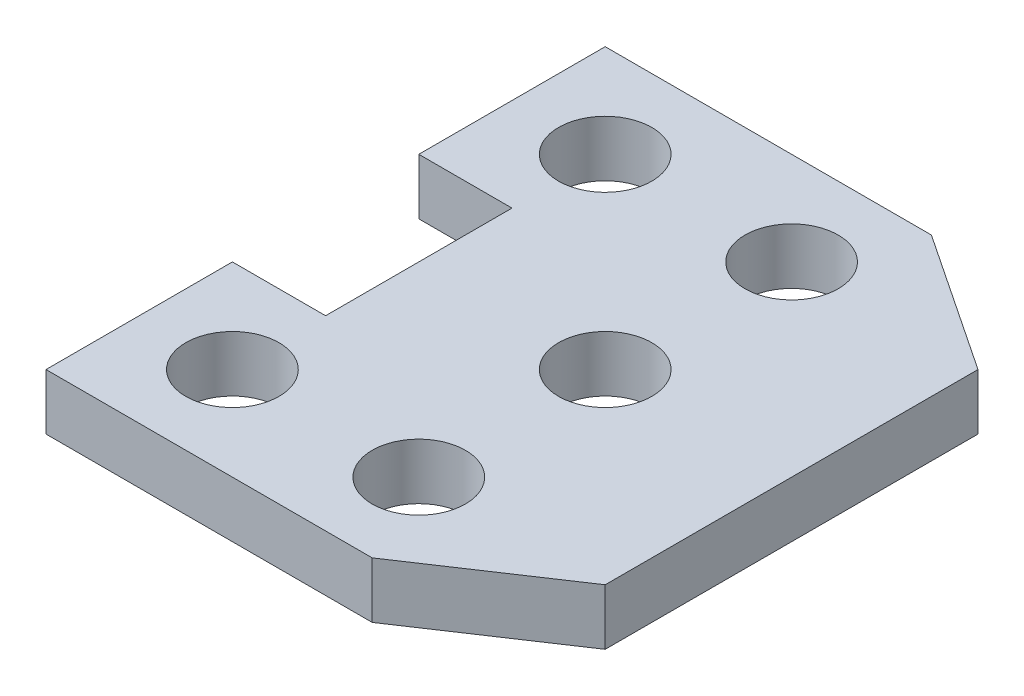
SolidWorks part; units mm, degrees
ref_plane "Front Plane" through (0, 0, 0) normal (0, 0, 1) x (1, 0, 0)
ref_plane "Top Plane" through (0, 0, 0) normal (0, 1, 0) x (1, 0, 0)
ref_plane "Right Plane" through (0, 0, 0) normal (1, 0, 0) x (0, 0, -1)
sketch "Sketch3" plane through (0, 0, 0) normal (0, 1, 0) x (1, 0, 0)
  line L0 (0, 0) -> (-70, 0)
  line L1 (-70, 0) -> (-70, 40)
  line L2 (-70, 40) -> (-50, 40)
  line L3 (-50, 40) -> (-50, 80)
  line L4 (-50, 80) -> (-70, 80)
  line L5 (-70, 80) -> (-70, 120)
  line L6 (-70, 120) -> (0, 120)
  line L10 (30, 100) -> (30, 20)
  line L15 (0, 0) -> (30, 20)
  line L16 (0, 120) -> (30, 100)
  circle A0 centre (-50, 100) radius 10
  circle A1 centre (-10, 100) radius 10
  circle A2 centre (-50, 20) radius 10
  circle A3 centre (-10, 20) radius 10
  circle A4 centre (-10, 60) radius 10
  point P27 (-50, 60)
  dimension "D12" = 20
  dimension "D15" = 20
  dimension "D16" = 20
  dimension "D17" = 20
  dimension "D18" = 20
  dimension "D19" = 20
  dimension "D2" = 120
  dimension "D3" = 40
  dimension "D4" = 40
  dimension "D5" = 20
  dimension "D6" = 80
  dimension "D7" = 100
  dimension "D8" = 40
  dimension "D9" = 40
  dimension "D10" = 40
  dimension "D11" = 70
  dimension "D13" = 70
  dimension "D14" = 20
  dimension "D20" = 80
  dimension "D21" = 40
  dimension "D22" = 20
  dimension "D23" = 40
  dimension "D24" = 20
  dimension "D25" = 20
  dimension "D26" = 20
extrude "Boss-Extrude1" add sketch "Sketch3" along normal blind 12
